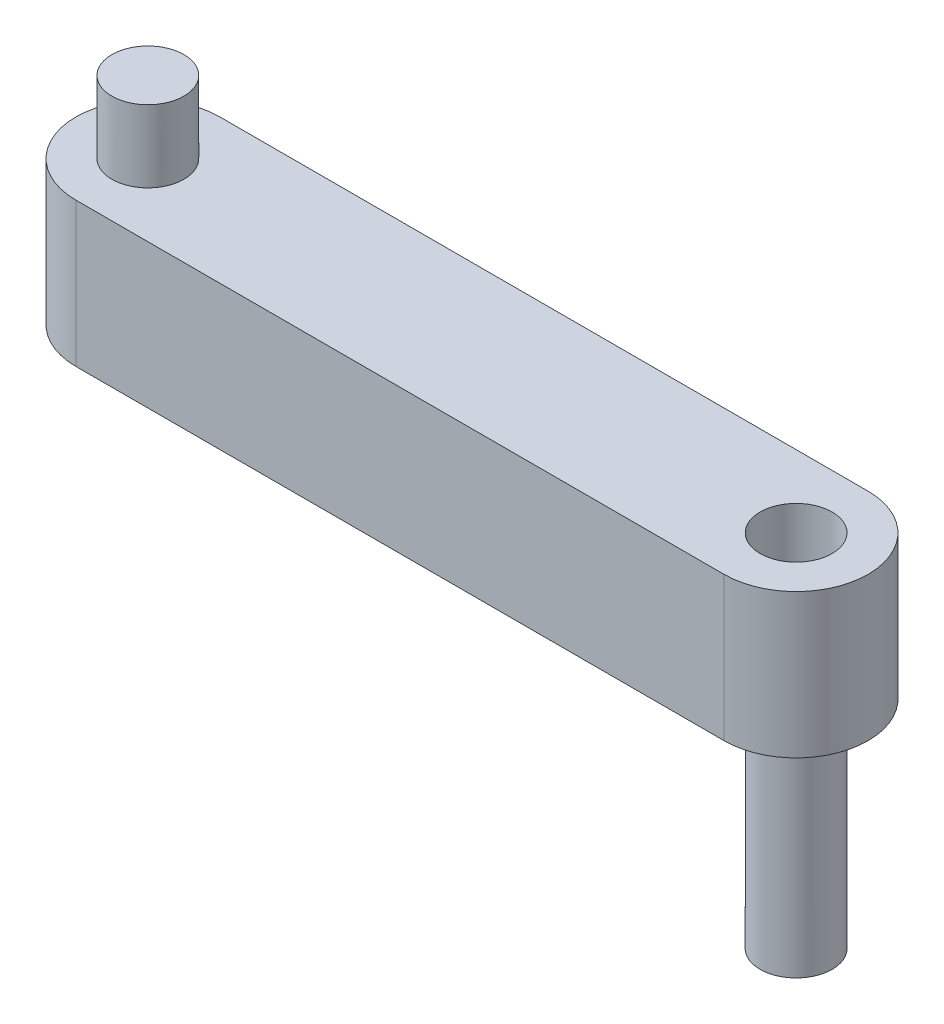
SolidWorks part; units mm, degrees
material "Crank"
ref_plane "Front Plane" through (0, 0, 0) normal (0, 0, 1) x (1, 0, 0)
ref_plane "Top Plane" through (0, 0, 0) normal (0, 1, 0) x (1, 0, 0)
ref_plane "Right Plane" through (0, 0, 0) normal (1, 0, 0) x (0, 0, -1)
sketch "Sketch1" plane through (0, 0, 0) normal (0, 1, 0) x (1, 0, 0)
  line L0 (-22.5, -5) -> (22.5, -5)
  line L1 (-22.5, 5) -> (22.5, 5)
  line L2 (0, 0) -> (0, 59.1545) construction
  line L3 (0, 0) -> (122.9641, 0) construction
  line L4 (0, 0) -> (-105.8579, 0) construction
  line L5 (0, 0) -> (0, -59.5641) construction
  arc A0 (22.5, -5) -> (22.5, 5) centre (22.5, 0) ccw
  arc A1 (-22.5, -5) -> (-22.5, 5) centre (-22.5, 0) cw
  dimension "D1" = 22.5
  dimension "D2" = 45
  dimension "D3" = 22.5
  dimension "D4" = 22.5
  dimension "D5" = 22.5
  dimension "D6" = 10
  dimension "D7" = 5
extrude "Boss-Extrude1" add sketch "Sketch1" along normal blind 10
sketch "Sketch2" plane through (0, 10, 0) normal (0, 1, 0) x (1, 0, 0)
  line L0 (22.5, 5) -> (-22.5, 5) construction
  circle A0 centre (-22.5, 0) radius 2.5
  dimension "D1" = 5
  dimension "D2" = 22.5
sketch "Sketch3" plane through (0, 10, 0) normal (0, 1, 0) x (1, 0, 0)
  line L0 (22.5, 5) -> (-22.5, 5) construction
  circle A0 centre (22.5, 0) radius 2.5
  dimension "D1" = 5
  dimension "D2" = 22.5
extrude "Boss-Extrude2" add sketch "Sketch2" along normal blind 5
extrude "Boss-Extrude3" add sketch "Sketch3" against normal blind 25
sketch "Sketch4" plane through (0, 10, 0) normal (0, 1, 0) x (1, 0, 0)
  line L0 (22.5, 5) -> (-22.5, 5) construction
  circle A0 centre (22.5, 0) radius 2.5
  dimension "D1" = 5
  dimension "D2" = 22.5
sketch "Sketch5" plane through (0, 0, 0) normal (0, -1, 0) x (1, 0, 0)
  line L0 (22.5, -5) -> (-22.5, -5) construction
  circle A0 centre (-22.5, 0) radius 2.5
  dimension "D1" = 5
  dimension "D2" = 22.5
extrude "Cut-Extrude1" cut sketch "Sketch5" against normal blind 5
extrude "Cut-Extrude2" cut sketch "Sketch4" against normal blind 5
